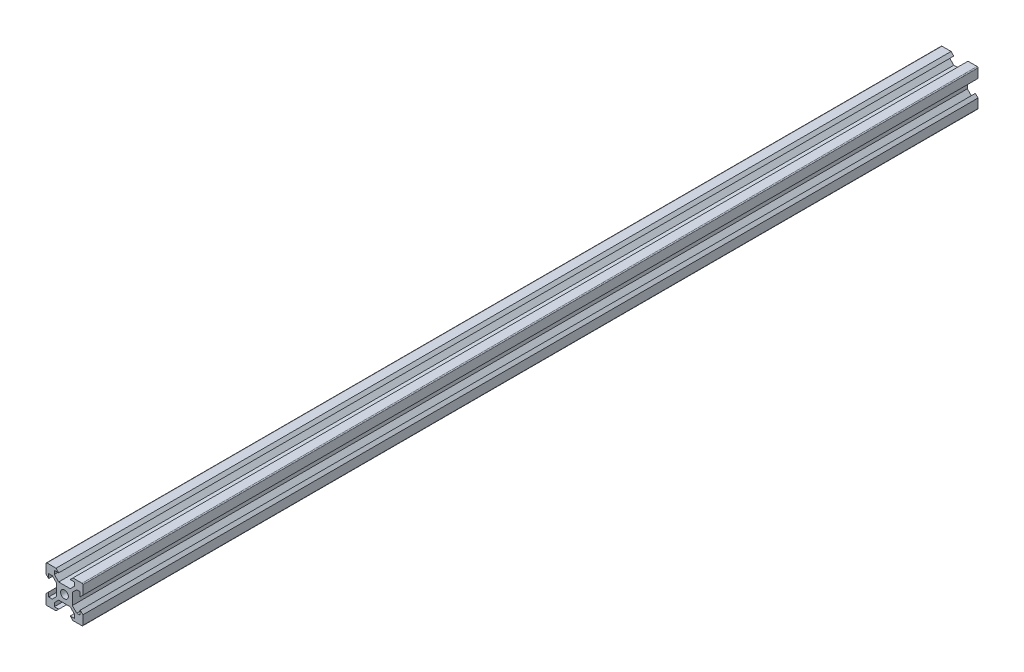
SolidWorks part; units mm, degrees
ref_plane "Front Plane" through (0, 0, 0) normal (0, 0, 1) x (1, 0, 0)
ref_plane "Top Plane" through (0, 0, 0) normal (0, 1, 0) x (1, 0, 0)
ref_plane "Right Plane" through (0, 0, 0) normal (1, 0, 0) x (0, 0, -1)
sketch "Sketch1" plane through (0, 0, 0) normal (0, 0, 1) x (1, 0, 0)
  line L0 (-3.125, 4.245) -> (3.125, 4.245)
  line L1 (3.125, 4.245) -> (5.5, 6.62)
  line L2 (5.5, 6.62) -> (5.5, 8.545)
  line L3 (5.5, 8.545) -> (3.125, 8.545)
  line L4 (3.125, 8.545) -> (4.58, 10)
  line L5 (4.58, 10) -> (9.5, 10)
  line L6 (10, 9.5) -> (10, 4.58)
  line L7 (10, 4.58) -> (8.545, 3.125)
  line L8 (8.545, 3.125) -> (8.545, 5.5)
  line L9 (8.545, 5.5) -> (6.62, 5.5)
  line L10 (6.62, 5.5) -> (4.245, 3.125)
  line L11 (4.245, 3.125) -> (4.245, -3.125)
  line L12 (0, 0) -> (-9.4136, 0) construction
  line L13 (0, 0) -> (0, -8.8273) construction
  line L14 (-4.245, 3.125) -> (-4.245, -3.125)
  line L15 (-6.62, 5.5) -> (-4.245, 3.125)
  line L16 (-8.545, 5.5) -> (-6.62, 5.5)
  line L17 (-8.545, 3.125) -> (-8.545, 5.5)
  line L18 (-10, 4.58) -> (-8.545, 3.125)
  line L19 (-10, 9.5) -> (-10, 4.58)
  line L20 (-4.58, 10) -> (-9.5, 10)
  line L21 (-3.125, 8.545) -> (-4.58, 10)
  line L22 (-5.5, 8.545) -> (-3.125, 8.545)
  line L23 (-5.5, 6.62) -> (-5.5, 8.545)
  line L24 (-3.125, 4.245) -> (-5.5, 6.62)
  line L25 (-3.125, -4.245) -> (-5.5, -6.62)
  line L26 (-5.5, -6.62) -> (-5.5, -8.545)
  line L27 (-5.5, -8.545) -> (-3.125, -8.545)
  line L28 (-3.125, -8.545) -> (-4.58, -10)
  line L29 (-4.58, -10) -> (-9.5, -10)
  line L30 (-10, -9.5) -> (-10, -4.58)
  line L31 (-10, -4.58) -> (-8.545, -3.125)
  line L32 (-8.545, -3.125) -> (-8.545, -5.5)
  line L33 (-8.545, -5.5) -> (-6.62, -5.5)
  line L34 (-6.62, -5.5) -> (-4.245, -3.125)
  line L35 (6.62, -5.5) -> (4.245, -3.125)
  line L36 (8.545, -5.5) -> (6.62, -5.5)
  line L37 (8.545, -3.125) -> (8.545, -5.5)
  line L38 (10, -4.58) -> (8.545, -3.125)
  line L39 (10, -9.5) -> (10, -4.58)
  line L40 (4.58, -10) -> (9.5, -10)
  line L41 (3.125, -8.545) -> (4.58, -10)
  line L42 (5.5, -8.545) -> (3.125, -8.545)
  line L43 (5.5, -6.62) -> (5.5, -8.545)
  line L44 (3.125, -4.245) -> (5.5, -6.62)
  line L45 (-3.125, -4.245) -> (3.125, -4.245)
  circle A0 centre (0, 0) radius 2.1
  arc A1 (10, 9.5) -> (9.5, 10) centre (9.5, 9.5) ccw
  arc A2 (-10, 9.5) -> (-9.5, 10) centre (-9.5, 9.5) cw
  arc A3 (-10, -9.5) -> (-9.5, -10) centre (-9.5, -9.5) ccw
  arc A4 (10, -9.5) -> (9.5, -10) centre (9.5, -9.5) cw
  point P3 (-10, 10)
  point P18 (10, 10)
  point P35 (0, 4.245)
  point P37 (4.245, 0)
  point P38 (-4.245, 0)
  point P62 (0, -4.245)
  point P63 (10, -10)
  point P64 (-10, -10)
  dimension "D1" = 4.2
  dimension "D17" = 0.5
  dimension "D2" = 10
  dimension "D3" = 10
  dimension "D4" = 45
  dimension "D5" = 3.125
  dimension "D6" = 3.125
  dimension "D7" = 4.58
  dimension "D8" = 4.58
  dimension "D9" = 5.5
  dimension "D10" = 5.5
  dimension "D13" = 3.125
  dimension "D14" = 3.125
  dimension "D15" = 4.3
  dimension "D16" = 4.3
extrude "Boss-Extrude1" add sketch "Sketch1" along normal blind 485
sketch "Sketch2" plane through (-4.245, 0, 0) normal (-1, 0, 0) x (0, 0, 1)
  line L0 (485, 3.125) -> (0, 3.125) construction
  line L1 (485, 3.125) -> (485, -3.125) construction
  line L2 (485, 3.125) -> (0, 3.125) construction
  circle A0 centre (8, 0) radius 1.5
  circle A1 centre (478.45, 0) radius 1.5
  circle A2 centre (68.5, 0) radius 1.5
  circle A3 centre (417.95, 0) radius 1.5
  dimension "D1" = 3
  dimension "D3" = 3.125
  dimension "D4" = 3
  dimension "D8" = 3
  dimension "D11" = 3
  dimension "D2" = 8
  dimension "D5" = 6.55
  dimension "D6" = 3.125
  dimension "D7" = 60.5
  dimension "D9" = 3.125
  dimension "D10" = 60.5
  dimension "D12" = 3.125
extrude "Cut-Extrude1" cut sketch "Sketch2" against normal up to next
